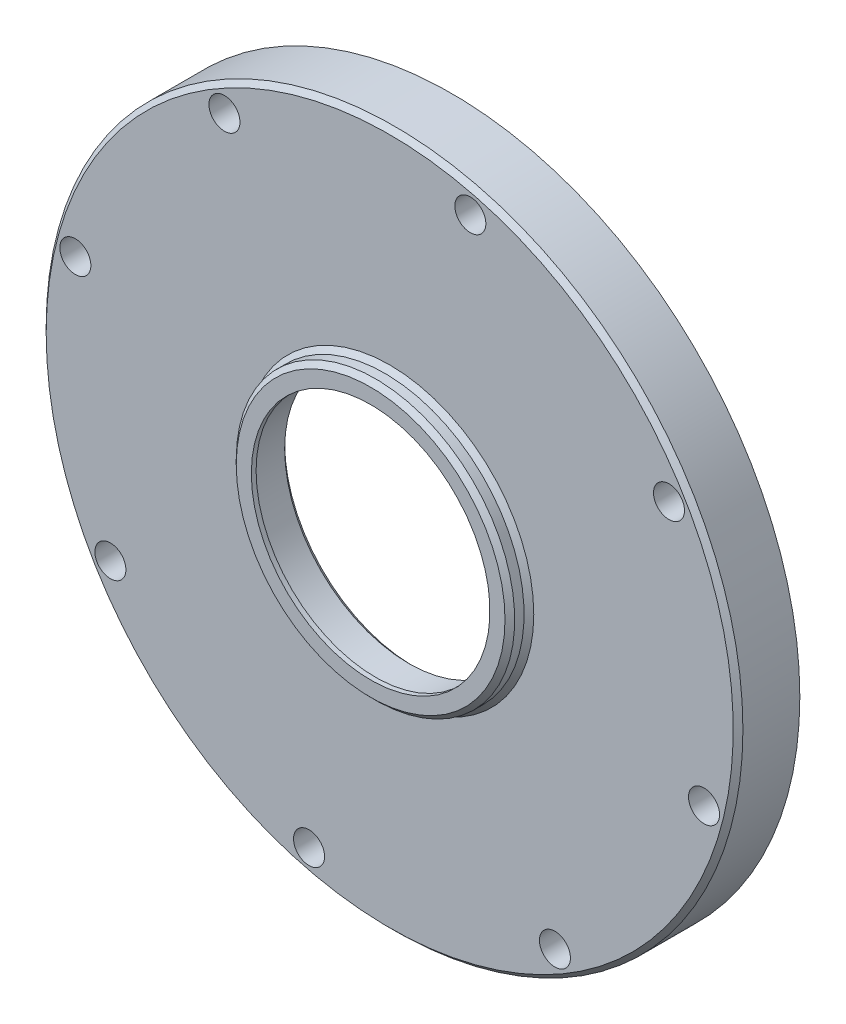
SolidWorks part; units mm, degrees
material "6061-T6 (SS)"
ref_plane "Front Plane" through (0, 0, 0) normal (0, 0, 1) x (1, 0, 0)
ref_plane "Top Plane" through (0, 0, 0) normal (0, 1, 0) x (1, 0, 0)
ref_plane "Right Plane" through (0, 0, 0) normal (1, 0, 0) x (0, 0, -1)
ref_axis "Axis1" through (0, 0, 0) along (0, 0, 1)
sketch "Sketch1" plane through (0, 0, 0) normal (1, 0, 0) x (0, 0, -1)
  line L0 (0.8617, -29.175) -> (0.0489, -29.175)
  line L1 (-0.1543, -26) -> (0.8617, -27.016)
  line L2 (-7.1383, -26) -> (-7.1383, -25)
  line L3 (0.8617, -29.175) -> (0.8617, -27.016)
  line L4 (-0.9671, -30.191) -> (-0.9671, -61.484)
  line L5 (-0.1543, -26) -> (-7.1383, -26)
  line L6 (-7.1383, -25) -> (-8.1383, -25)
  line L7 (0.0489, -62.5) -> (8.7992, -62.5)
  line L8 (8.7992, -62.5) -> (8.7992, -73)
  line L9 (8.7992, -73) -> (-3.1261, -73)
  line L10 (-5.1581, -29.175) -> (-4.1421, -30.191)
  line L11 (-8.1383, -28.159) -> (-7.1223, -29.175)
  line L12 (0.0489, -29.175) -> (-0.9671, -30.191)
  line L13 (-3.1261, -73) -> (-4.1421, -71.984)
  line L14 (-0.9671, -61.484) -> (0.0489, -62.5)
  line L16 (-7.1223, -29.175) -> (-5.1581, -29.175)
  line L17 (-4.1421, -30.191) -> (-4.1421, -71.984)
  line L20 (-8.1383, -25) -> (-8.1383, -28.159)
  point P1 (-0.9671, -29.175)
  point P2 (-0.9671, -62.5)
  point P4 (0.8617, -26)
  point P13 (-8.1383, -29.175)
  point P15 (-4.1421, -29.175)
  point P16 (-4.1421, -73)
  dimension "D1" = 26
  dimension "D2" = 1
  dimension "D3" = 16.9375
  dimension "D4" = 8
  dimension "D5" = 62.5
  dimension "D6" = 73
  dimension "D7" = 12.9413
  dimension "D8" = 3.175
  dimension "D9" = 1
  dimension "D10" = 3.175
revolve "Revolve1" add sketch "Sketch1" angle 360 about axis through (0, 0, 0) along (0, 0, 1)
sketch "Sketch2" plane through (0, 0, 0) normal (0, 0, 1) x (1, 0, 0)
  circle A0 centre (-58.5244, -34.625) radius 3.25
  circle A1 centre (0, 0) radius 68 construction
  circle A3 centre (-65.8666, 16.8994) radius 3.25
  circle A4 centre (-34.625, 58.5244) radius 3.25
  circle A5 centre (16.8994, 65.8666) radius 3.25
  circle A6 centre (58.5244, 34.625) radius 3.25
  circle A7 centre (65.8666, -16.8994) radius 3.25
  circle A8 centre (34.625, -58.5244) radius 3.25
  circle A9 centre (-16.8994, -65.8666) radius 3.25
  point P22 (0, 0)
  dimension "D1" = 6.5
  dimension "D2" = 136
  dimension "D3" = 8
extrude "Cut-Extrude1" cut sketch "Sketch2" along normal through all both and the other way through all contours A0
